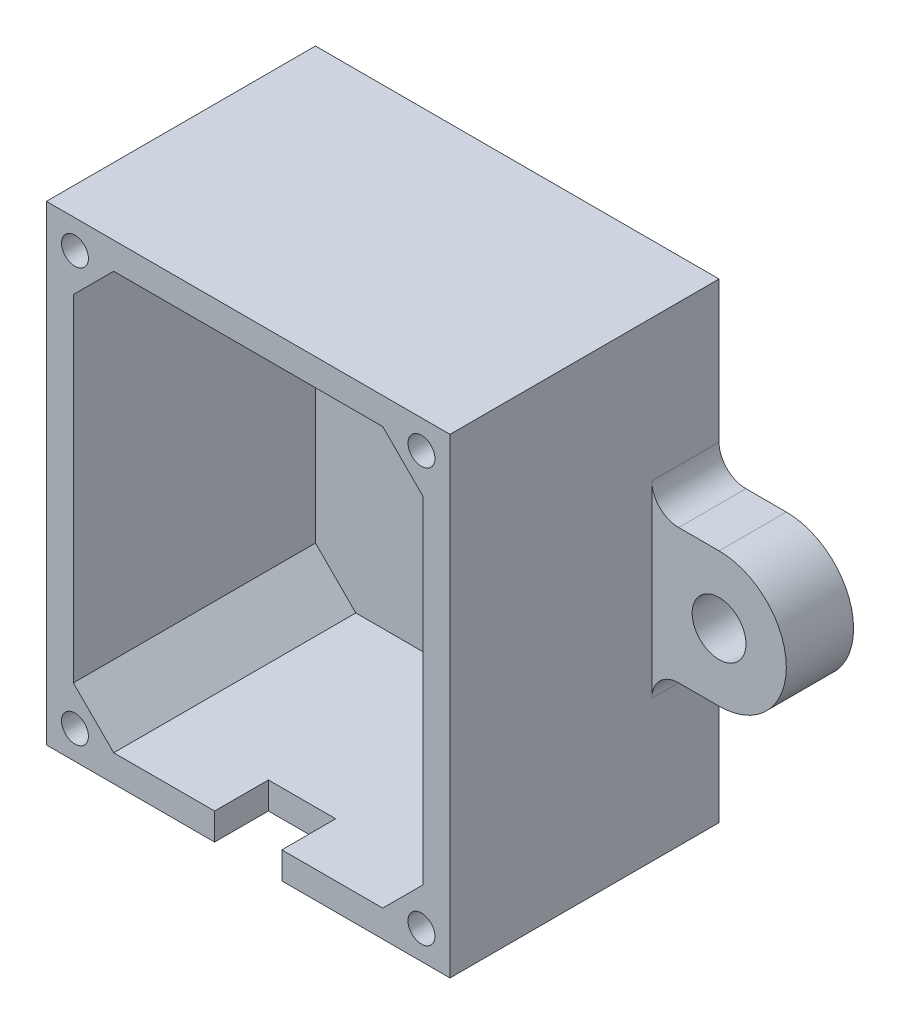
SolidWorks part; units mm, degrees
ref_plane "Plan de face" through (0, 0, 0) normal (0, 0, 1) x (1, 0, 0)
ref_plane "Plan de dessus" through (0, 0, 0) normal (0, 1, 0) x (1, 0, 0)
ref_plane "Plan de droite" through (0, 0, 0) normal (1, 0, 0) x (0, 0, -1)
sketch "Esquisse1" plane through (0, 0, 0) normal (0, 0, 1) x (1, 0, 0)
  line L1 (-15, 17.5) -> (15, 17.5)
  line L2 (-15, 17.5) -> (-15, -17.5)
  line L3 (-15, -17.5) -> (15, -17.5)
  line L4 (15, 17.5) -> (15, -17.5)
  point P4 (0, -17.5)
  point P6 (-15, 0)
  dimension "D1" = 30
  dimension "D2" = 35
extrude "Boss.-Extru.1" add sketch "Esquisse1" along normal blind 20
sketch "Esquisse2" plane through (0, 0, 20) normal (0, 0, 1) x (1, 0, 0)
  line L1 (-10, 15.5) -> (10, 15.5)
  line L2 (13, 12.5) -> (13, -12.5)
  line L4 (10, -15.5) -> (-10, -15.5)
  line L8 (-10, 15.5) -> (-13, 12.5)
  line L9 (-13, -12.5) -> (-10, -15.5)
  line L10 (10, -15.5) -> (13, -12.5)
  line L11 (10, 15.5) -> (13, 12.5)
  line L12 (-13, -12.5) -> (-13, 12.5)
  line L13 (15, 17.5) -> (-15, 17.5) construction
  line L14 (-15, -17.5) -> (15, -17.5) construction
  line L15 (15, -17.5) -> (15, 17.5) construction
  line L16 (-15, 17.5) -> (-15, -17.5) construction
  dimension "D1" = 2
  dimension "D2" = 2
  dimension "D3" = 2
  dimension "D4" = 2
  dimension "D5" = 3
  dimension "D6" = 3
  dimension "D7" = 3
  dimension "D8" = 3
  dimension "D9" = 3
  dimension "D10" = 3
  dimension "D11" = 3
  dimension "D12" = 3
extrude "Enlèv. mat.-Extru.1" cut sketch "Esquisse2" against normal blind 18
sketch "Esquisse3" plane through (0, 0, 0) normal (0, 0, -1) x (-1, 0, 0)
  line L0 (-15, 5) -> (-20, 5)
  line L1 (-15, -17.5) -> (-15, 17.5) construction
  line L2 (-20, -5) -> (-15, -5)
  line L3 (-15, 5) -> (-15, -5)
  line L4 (0, 0) -> (0, -13.3117) construction
  line L5 (15, 5) -> (15, -5)
  line L6 (20, -5) -> (15, -5)
  line L7 (15, 5) -> (20, 5)
  arc A0 (-20, 5) -> (-20, -5) centre (-20, 0) ccw
  arc A1 (20, 5) -> (20, -5) centre (20, 0) cw
  dimension "D2" = 5
  dimension "D1" = 5
extrude "Boss.-Extru.2" add sketch "Esquisse3" against normal blind 5
sketch "Esquisse4" plane through (0, 0, 5) normal (0, 0, 1) x (1, 0, 0)
  circle A0 centre (-20, 0) radius 2
  circle A1 centre (20, 0) radius 2
  arc A2 (-20, 5) -> (-20, -5) centre (-20, 0) ccw construction
  arc A3 (20, -5) -> (20, 5) centre (20, 0) ccw construction
  dimension "D1" = 4
extrude "Enlèv. mat.-Extru.2" cut sketch "Esquisse4" against normal up to next
sketch "Esquisse5" plane through (0, 0, 2) normal (0, 0, 1) x (1, 0, 0)
  line L3 (-10, 15.5) -> (10, 15.5)
  line L4 (-10, 15.5) -> (-10, 5.5)
  line L5 (-10, 5.5) -> (10, 5.5)
  line L6 (10, 15.5) -> (10, 5.5)
  dimension "D1" = 10
extrude "Boss.-Extru.3" add sketch "Esquisse5" along normal blind 5
sketch "Esquisse6" plane through (0, -17.5, 0) normal (0, -1, 0) x (1, 0, 0)
  line L0 (-15, 20) -> (15, 20) construction
  line L1 (-2.5, 20) -> (2.5, 20)
  line L2 (-2.5, 20) -> (-2.5, 16)
  line L3 (-2.5, 16) -> (2.5, 16)
  line L4 (2.5, 20) -> (2.5, 16)
  point P6 (0, 16)
  dimension "D1" = 4
  dimension "D2" = 5
extrude "Enlèv. mat.-Extru.3" cut sketch "Esquisse6" against normal up to next
fillet "Congé1" radius 2 4 edges
sketch "Esquisse7" plane through (0, 0, 20) normal (0, 0, 1) x (1, 0, 0)
  line L0 (-15, 17.5) -> (-11.5, 14) construction
  line L1 (-10, 15.5) -> (-13, 12.5) construction
  line L2 (15, 17.5) -> (11.5, 14) construction
  line L3 (13, 12.5) -> (10, 15.5) construction
  line L4 (11.5, -14) -> (15, -17.5) construction
  line L5 (10, -15.5) -> (13, -12.5) construction
  line L6 (-11.5, -14) -> (-15, -17.5) construction
  line L7 (-13, -12.5) -> (-10, -15.5) construction
  circle A0 centre (-12.8787, 15.3787) radius 1
  circle A1 centre (-12.8787, -15.3787) radius 1
  circle A2 centre (12.8787, -15.3787) radius 1
  circle A3 centre (12.8787, 15.3787) radius 1
  point P24 (-13.25, -15.75)
  dimension "D1" = 2
  dimension "D3" = 3
  dimension "D2" = 3
  dimension "D4" = 3
  dimension "D5" = 3
extrude "Enlèv. mat.-Extru.4" cut sketch "Esquisse7" against normal blind 10
